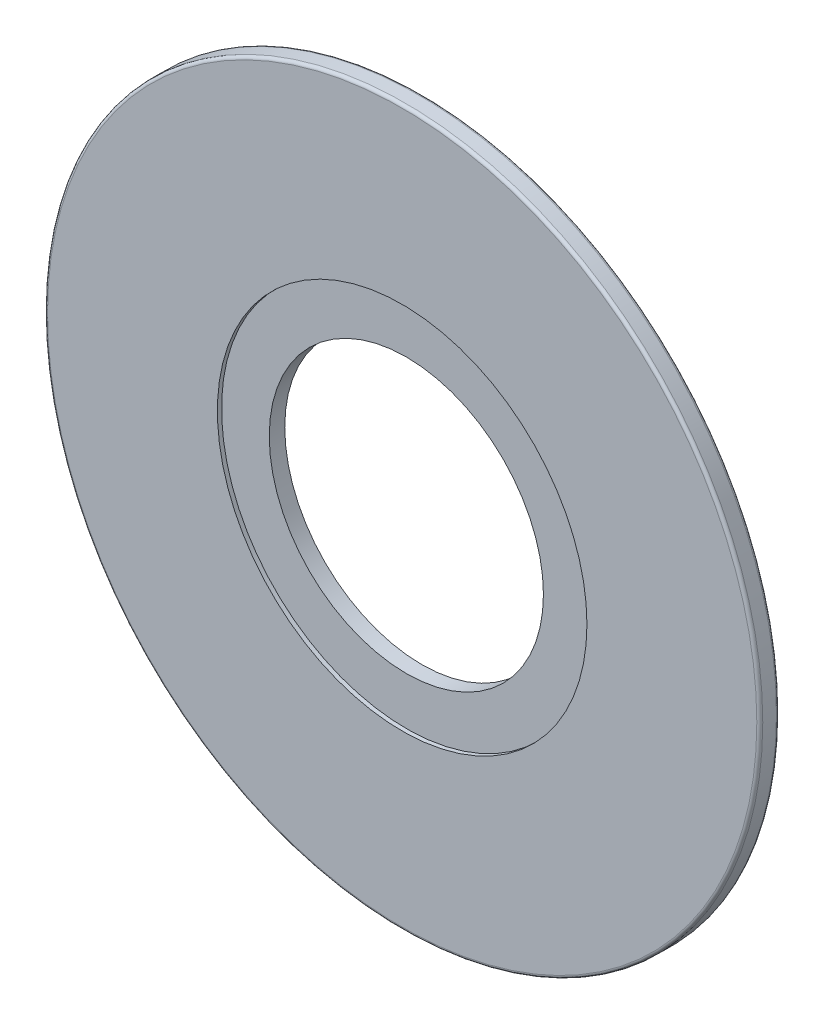
SolidWorks part; units mm, degrees
ref_plane "Plano frontal" through (0, 0, 0) normal (0, 0, 1) x (1, 0, 0)
ref_plane "Plano superior" through (0, 0, 0) normal (0, 1, 0) x (1, 0, 0)
ref_plane "Plano direito" through (0, 0, 0) normal (1, 0, 0) x (0, 0, -1)
sketch "Esboço1" plane through (0, 0, 0) normal (0, 0, 1) x (1, 0, 0)
  circle A0 centre (0, 0) radius 30
  dimension "D1" = 60
extrude "Ressalto-extrusão1" add sketch "Esboço1" along normal blind 2
sketch "Esboço2" plane through (0, 0, 0) normal (0, 0, -1) x (-1, 0, 0)
  line L1 (-17.4622, -20.593) -> (-9.6118, -12.1599)
  line L2 (-1.25, -26.971) -> (-1.25, -15.4495)
  line L4 (1.25, -26.971) -> (1.25, -15.4495)
  line L7 (-26.971, -1.25) -> (-15.4495, -1.25)
  line L9 (-26.971, 1.25) -> (-15.4495, 1.25)
  line L10 (-19.292, -18.8896) -> (-11.4417, -10.4565)
  line L18 (19.3348, -18.8459) -> (10.7207, -11.1945)
  line L21 (20.995, -16.9767) -> (12.3809, -9.3254)
  line L30 (15.4495, -1.25) -> (26.971, -1.25)
  line L33 (15.4495, 1.25) -> (26.971, 1.25)
  line L34 (11.4417, 10.4565) -> (19.292, 18.8896)
  line L37 (9.6118, 12.1599) -> (17.4622, 20.593)
  line L38 (1.25, 15.4495) -> (1.25, 26.971)
  line L41 (-1.25, 15.4495) -> (-1.25, 26.971)
  line L42 (-10.7207, 11.1945) -> (-19.3348, 18.8459)
  line L45 (-12.3809, 9.3254) -> (-20.995, 16.9767)
  circle A0 centre (0, 0) radius 30
  arc A1 (17.4622, 20.593) -> (1.25, 26.971) centre (0, 0) ccw
  circle A2 centre (0, 0) radius 11.5
  arc A3 (-9.6118, -12.1599) -> (-1.25, -15.4495) centre (0, 0) ccw
  arc A4 (-15.4495, -1.25) -> (-11.4417, -10.4565) centre (0, 0) ccw
  arc A5 (15.4495, 1.25) -> (11.4417, 10.4565) centre (0, 0) ccw
  arc A6 (12.3809, -9.3254) -> (15.4495, -1.25) centre (0, 0) ccw
  arc A7 (1.25, -15.4495) -> (10.7207, -11.1945) centre (0, 0) ccw
  arc A8 (-1.25, 15.4495) -> (-10.7207, 11.1945) centre (0, 0) ccw
  arc A9 (9.6118, 12.1599) -> (1.25, 15.4495) centre (0, 0) ccw
  arc A10 (-12.3809, 9.3254) -> (-15.4495, 1.25) centre (0, 0) ccw
  arc A11 (-1.25, 26.971) -> (-19.3348, 18.8459) centre (0, 0) ccw
  arc A12 (-20.995, 16.9767) -> (-26.971, 1.25) centre (0, 0) ccw
  arc A13 (26.971, 1.25) -> (19.292, 18.8896) centre (0, 0) ccw
  arc A14 (20.995, -16.9767) -> (26.971, -1.25) centre (0, 0) ccw
  arc A15 (-26.971, -1.25) -> (-19.292, -18.8896) centre (0, 0) ccw
  arc A16 (-17.4622, -20.593) -> (-1.25, -26.971) centre (0, 0) ccw
  arc A17 (1.25, -26.971) -> (19.3348, -18.8459) centre (0, 0) ccw
  dimension "D1" = 3
  dimension "D2" = 60
  dimension "D3" = 23
  dimension "D4" = 4
extrude "Corte-extrusão6" cut sketch "Esboço2" against normal blind 0.35
sketch "Esboço9" plane through (0, 0, 0) normal (0, 0, -1) x (-1, 0, 0)
  circle A0 centre (0, 0) radius 11.5
  dimension "D1" = 23
extrude "Corte-extrusão7" cut sketch "Esboço9" against normal blind 12.35 and the other way blind 37
fillet "Filete2" radius 0.25 2 edges at (-30, 0, 0.35) (30, 0, 2)
sketch "Esboço10" plane through (0, 0, 2) normal (0, 0, 1) x (1, 0, 0)
  circle A0 centre (0, 0) radius 15.5
  dimension "D1" = 31
extrude "Corte-extrusão8" cut sketch "Esboço10" against normal blind 0.35
